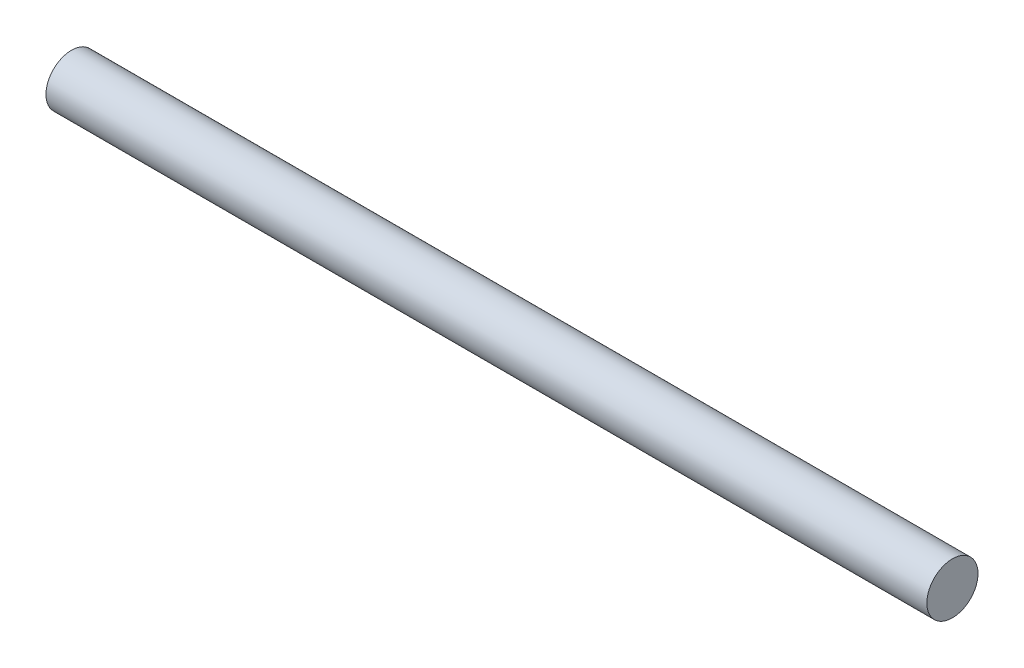
SolidWorks part; units mm, degrees
ref_plane "Plan de face" through (0, 0, 0) normal (0, 0, 1) x (1, 0, 0)
ref_plane "Plan de dessus" through (0, 0, 0) normal (0, 1, 0) x (1, 0, 0)
ref_plane "Plan de droite" through (0, 0, 0) normal (1, 0, 0) x (0, 0, -1)
sketch "Esquisse5" plane through (0, 0, 0) normal (1, 0, 0) x (0, 0, -1)
  circle A0 centre (0, 0) radius 18
extrude "Boss.-Extru.3" add sketch "Esquisse5" along normal blind 620
ref_plane "Plan2" through (10, 0, 0) normal (-1, 0, 0) x (0, 0, 1)
ref_plane "Plan4" through (610, 0, 0) normal (-1, 0, 0) x (0, 0, 1)
sketch "Esquisse6" plane through (10, 0, 0) normal (-1, 0, 0) x (0, 0, 1)
  circle A0 centre (0, 0) radius 18
sketch "Esquisse7" plane through (610, 0, 0) normal (-1, 0, 0) x (0, 0, 1)
  circle A0 centre (0, 0) radius 18
ref_plane "Plan31" through (524, 0, 0) normal (-1, 0, 0) x (0, 0, 1)
sketch "Esquisse32" plane through (524, 0, 0) normal (-1, 0, 0) x (0, 0, 1)
  circle A0 centre (0, 0) radius 18
ref_plane "Plan32" through (438, 0, 0) normal (-1, 0, 0) x (0, 0, 1)
ref_plane "Plan33" through (352, 0, 0) normal (-1, 0, 0) x (0, 0, 1)
ref_plane "Plan34" through (266, 0, 0) normal (-1, 0, 0) x (0, 0, 1)
ref_plane "Plan35" through (180, 0, 0) normal (-1, 0, 0) x (0, 0, 1)
ref_plane "Plan36" through (94, 0, 0) normal (-1, 0, 0) x (0, 0, 1)
sketch "Esquisse33" plane through (438, 0, 0) normal (-1, 0, 0) x (0, 0, 1)
  circle A0 centre (0, 0) radius 18
  circle A1 centre (0, 0) radius 18
sketch "Esquisse34" plane through (352, 0, 0) normal (-1, 0, 0) x (0, 0, 1)
  circle A0 centre (0, 0) radius 18
sketch "Esquisse35" plane through (180, 0, 0) normal (-1, 0, 0) x (0, 0, 1)
  circle A0 centre (0, 0) radius 18
sketch "Esquisse36" plane through (94, 0, 0) normal (-1, 0, 0) x (0, 0, 1)
  circle A0 centre (0, 0) radius 18
sketch "Esquisse37" plane through (266, 0, 0) normal (-1, 0, 0) x (0, 0, 1)
  circle A0 centre (0, 0) radius 18
